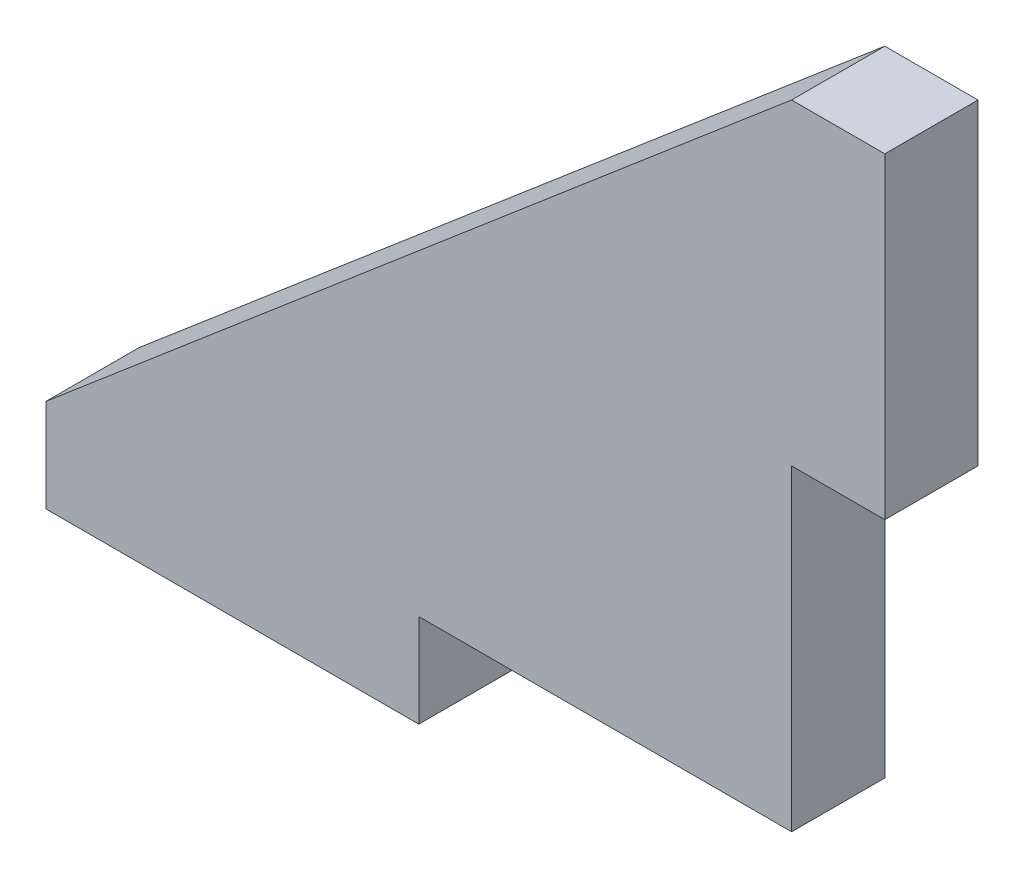
SolidWorks part; units mm, degrees
ref_plane "Alzado" through (0, 0, 0) normal (0, 0, 1) x (1, 0, 0)
ref_plane "Planta" through (0, 0, 0) normal (0, 1, 0) x (1, 0, 0)
ref_plane "Vista lateral" through (0, 0, 0) normal (1, 0, 0) x (0, 0, -1)
sketch "Croquis1" plane through (0, 0, 0) normal (0, 0, 1) x (1, 0, 0)
  line L0 (0, 0) -> (40, 34)
  line L1 (40, 34) -> (40, 0)
  line L2 (40, 0) -> (0, 0)
  line L4 (40, 34) -> (45, 34)
  line L5 (40, 34) -> (40, 17)
  line L6 (40, 17) -> (45, 17)
  line L7 (45, 34) -> (45, 17)
  line L8 (0, 0) -> (20, 0)
  line L9 (0, 0) -> (0, -5)
  line L10 (0, -5) -> (20, -5)
  line L11 (20, 0) -> (20, -5)
  point P7 (40, 17)
  point P12 (20, 0)
  dimension "D1" = 40
  dimension "D2" = 34
  dimension "D3" = 5
  dimension "D4" = 5
extrude "Saliente-Extruir1" add sketch "Croquis1" along normal blind 5 contours L7 L4 L1 L6 | L2 L1 L0 | L11 L2 L9 L10
sketch "Croquis2" plane through (0, 0, 5) normal (0, 0, 1) x (1, 0, 0)
  line L9 (45, 17) -> (45, 34)
  line L10 (45, 34) -> (40, 34)
  line L11 (40, 34) -> (0, 0)
  line L12 (0, 0) -> (0, -5)
  line L13 (0, -5) -> (20, -5)
  line L14 (20, -5) -> (20, 0)
  line L15 (20, 0) -> (40, 0)
  line L16 (40, 0) -> (40, 17)
  line L17 (40, 17) -> (45, 17)
  line L18 (45, 17) -> (45, 34)
  line L19 (45, 34) -> (40, 34)
  line L20 (40, 34) -> (0, 0)
  line L21 (0, 0) -> (0, -5)
  line L22 (0, -5) -> (20, -5)
  line L23 (20, -5) -> (20, 0)
  line L24 (20, 0) -> (40, 0)
  line L25 (40, 0) -> (40, 17)
  line L26 (40, 17) -> (45, 17)
  dimension "D1" = 0
